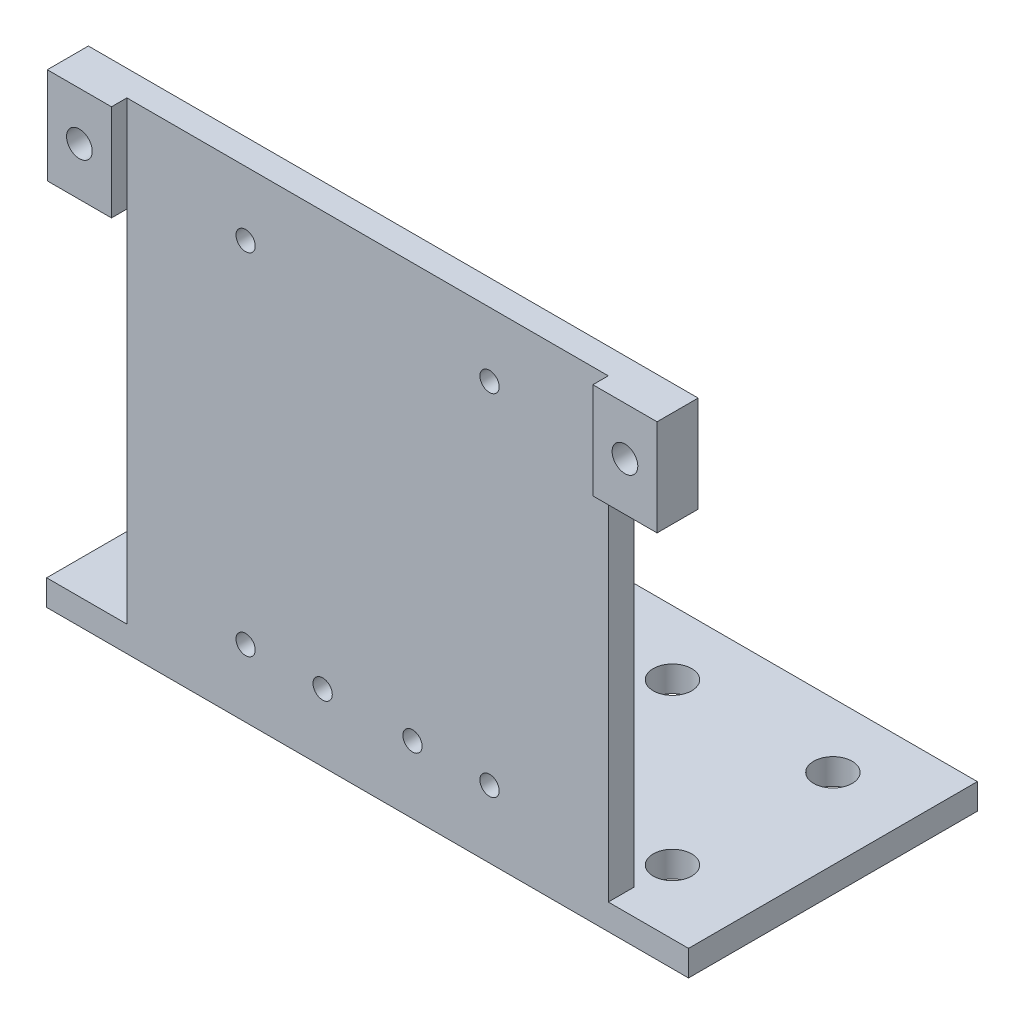
SolidWorks part; units mm, degrees
ref_plane "前视基准面" through (0, 0, 0) normal (0, 0, 1) x (1, 0, 0)
ref_plane "上视基准面" through (0, 0, 0) normal (0, 1, 0) x (1, 0, 0)
ref_plane "右视基准面" through (0, 0, 0) normal (1, 0, 0) x (0, 0, -1)
sketch "草图1" plane through (0, 0, 0) normal (0, 1, 0) x (1, 0, 0)
  line L0 (0, 0) -> (0, 10)
  line L1 (0, 0) -> (100, 0)
  line L2 (0, 0) -> (0, 45)
  line L3 (0, 45) -> (100, 45)
  line L4 (100, 0) -> (100, 45)
  line L5 (0, 10) -> (100, 10)
  line L6 (0, 10) -> (12.5, 10)
  line L7 (12.5, 10) -> (12.5, 35)
  line L8 (12.5, 35) -> (37.5, 35)
  line L9 (50, 22.5) -> (50, 10)
  line L10 (37.5, 35) -> (37.5, 10)
  circle A0 centre (12.5, 35) radius 3
  circle A1 centre (37.5, 35) radius 3
  circle A2 centre (37.5, 10) radius 3
  circle A3 centre (12.5, 10) radius 3
  circle A4 centre (62.5, 35) radius 3
  circle A5 centre (62.5, 10) radius 3
  circle A6 centre (87.5, 10) radius 3
  circle A7 centre (87.5, 35) radius 3
  point P4 (50, 22.5)
extrude "凸台-拉伸1" add sketch "草图1" along normal blind 4
sketch "草图2" plane through (0, 0, 0) normal (0, 0, 1) x (1, 0, 0)
  line L4 (0, 0) -> (12.5, 0)
  line L5 (0, 0) -> (100, 0) construction
  line L6 (12.5, 0) -> (12.5, 75)
  line L7 (12.5, 75) -> (2.5, 75)
  line L8 (2.5, 75) -> (2.5, 60)
  line L9 (2.5, 60) -> (12.5, 60)
  line L10 (50, 0) -> (50, 75)
  line L11 (87.5, 75) -> (12.5, 75)
  line L12 (12.5, 0) -> (87.5, 0)
  line L13 (12.5, 0) -> (31, 0)
  line L14 (31, 0) -> (31, 10.5)
  line L15 (31, 10.5) -> (43, 10.5)
  line L16 (31, 10.5) -> (31, 75)
  line L17 (31, 75) -> (31, 65)
  line L18 (2.5, 75) -> (12.5, 60)
  line L19 (12.5, 75) -> (2.5, 60)
  line L20 (12.5, 0) -> (87.5, 0)
  line L21 (87.5, 0) -> (87.5, 75)
  line L22 (97.5, 60) -> (87.5, 60)
  line L23 (97.5, 75) -> (97.5, 60)
  line L24 (87.5, 75) -> (97.5, 75)
  circle A0 centre (7.5, 67.5) radius 2
  circle A1 centre (31, 65) radius 1.5
  circle A2 centre (31, 10.5) radius 1.5
  circle A3 centre (43, 10.5) radius 1.5
  circle A4 centre (92.5, 67.5) radius 2
  circle A5 centre (57, 10.5) radius 1.5
  circle A6 centre (69, 10.5) radius 1.5
  circle A7 centre (69, 65) radius 1.5
extrude "凸台-拉伸2" add sketch "草图2" against normal blind 4
sketch "草图3" plane through (0, 0, 0) normal (0, 0, 1) x (1, 0, 0)
  line L1 (12.5, 60) -> (2.5, 60)
  line L2 (12.5, 60) -> (12.5, 75)
  line L3 (12.5, 75) -> (2.5, 75)
  line L4 (2.5, 60) -> (2.5, 75)
  line L5 (12.5, 60) -> (2.5, 75) construction
  line L6 (12.5, 75) -> (2.5, 60) construction
  line L7 (87.5, 60) -> (97.5, 60)
  line L8 (87.5, 60) -> (87.5, 75)
  line L9 (87.5, 75) -> (97.5, 75)
  line L10 (97.5, 60) -> (97.5, 75)
  line L11 (87.5, 60) -> (97.5, 75) construction
  line L12 (87.5, 75) -> (97.5, 60) construction
  circle A0 centre (7.5, 67.5) radius 2
  circle A1 centre (92.5, 67.5) radius 2
  point P4 (7.5, 67.5)
  point P11 (92.5, 67.5)
extrude "凸台-拉伸3" add sketch "草图3" along normal blind 2.4
sketch "草图4" plane through (87.5, 0, 0) normal (1, 0, 0) x (0, 0, -1)
  line L0 (4, 60) -> (4, 4)
  line L1 (0, 4) -> (45, 4) construction
  line L2 (4, 4) -> (0, 4) construction
  line L3 (4, 4) -> (12.5, 4)
  line L4 (12.5, 4) -> (4, 60)
extrude "凸台-拉伸4" add sketch "草图4" against normal blind 75
sketch "草图5" plane through (0, 0, 0) normal (0, 0, 1) x (1, 0, 0)
  circle A0 centre (31, 10.5) radius 1.5
  circle A1 centre (43, 10.5) radius 1.5
  circle A2 centre (57, 10.5) radius 1.5
  circle A3 centre (69, 10.5) radius 1.5
extrude "切除-拉伸1" cut sketch "草图5" against normal blind 75
sketch "草图6" plane through (0, 4, 0) normal (0, 1, 0) x (1, 0, 0)
  line L0 (12.5, 4) -> (21, 4)
  line L1 (12.5, 4) -> (87.5, 4) construction
  line L2 (21, 4) -> (25, 4)
  line L3 (25, 4) -> (25, 12.5)
  line L4 (14.1583, 12.5) -> (35.8417, 12.5) construction
  line L5 (25, 12.5) -> (21, 12.5)
  line L6 (21, 12.5) -> (21, 4)
  line L7 (21, 12.5) -> (12.5, 12.5)
  line L8 (12.5, 12.5) -> (12.5, 4)
  line L9 (87.5, 4) -> (79, 4)
  line L10 (97.5, 4) -> (2.5, 4) construction
  line L11 (79, 4) -> (75, 4)
  line L12 (87.5, 4) -> (87.5, 12.5)
  line L13 (87.5, 12.5) -> (79, 12.5)
  line L14 (64.1583, 12.5) -> (85.8417, 12.5) construction
  line L15 (79, 12.5) -> (79, 4)
  line L16 (79, 12.5) -> (75, 12.5)
  line L17 (75, 12.5) -> (75, 4)
  line L18 (25, 12.5) -> (75, 12.5)
  line L19 (75, 4) -> (25, 4)
  line M3 (64.1583, 12.5) -> (85.8417, 12.5)
  line M5 (87.5, 7) -> (87.5, 0)
  line M11 (12.5, 0) -> (12.5, 7)
  line M13 (14.1583, 12.5) -> (35.8417, 12.5)
  line M15 (39.1583, 12.5) -> (60.8417, 12.5)
extrude "切除-拉伸2" cut sketch "草图6" along normal blind 75 contours L7 L8 L0 L6 M11 M13 | L19 L17 L18 L3 M3 M15 M13 | L15 L9 L12 L13 M3 M5
